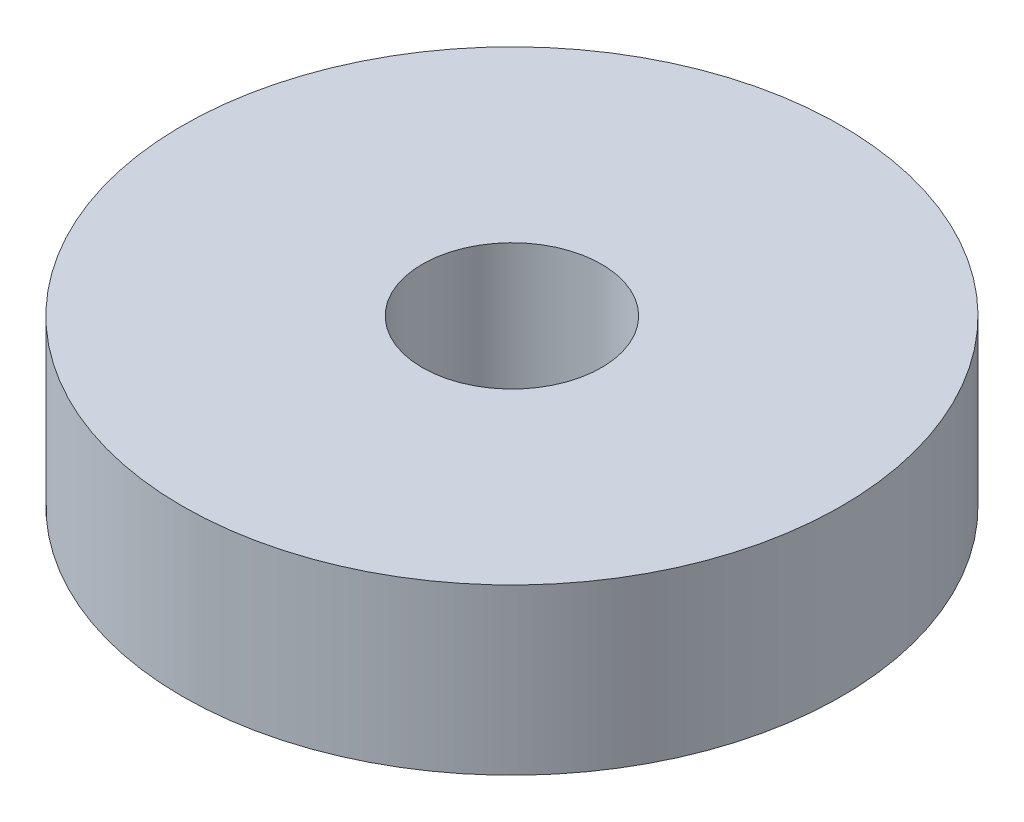
SolidWorks part; units mm, degrees
material "Acrylic (Medium-high impact)"
ref_plane "Front Plane" through (0, 0, 0) normal (0, 0, 1) x (1, 0, 0)
ref_plane "Top Plane" through (0, 0, 0) normal (0, 1, 0) x (1, 0, 0)
ref_plane "Right Plane" through (0, 0, 0) normal (1, 0, 0) x (0, 0, -1)
sketch "Sketch1" plane through (0, 0, 0) normal (0, 1, 0) x (1, 0, 0)
  circle A0 centre (0, 0) radius 6.35
  circle A1 centre (0, 0) radius 1.143
  dimension "D1" = 2.286
  dimension "D2" = 12.7
extrude "Boss-Extrude1" add sketch "Sketch1" along normal blind 3.175
hole_wizard "#8-32 Tapped Hole1" positions "Sketch3" profile "Sketch2" tap size "#8-32" standard "ANSI Inch" end condition through all
sketch "Sketch3" plane through (0, 3.175, 0) normal (0, 1, 0) x (1, 0, 0)
  point P0 (0, 0)
sketch "Sketch2" plane through (0, 3.175, 0) normal (1, 0, 0) x (0, 0, 1)
  line L0 (0, 0) -> (0, 3.175)
  line L1 (0, 3.175) -> (1.7272, 3.175)
  line L2 (1.7272, 3.175) -> (1.7272, 0)
  line L5 (1.7272, 0) -> (0, 0)
  line L11 (0, -6.35) -> (0, 107.95) construction
  dimension "Thru Tap Drill Dia." = 3.4544
  dimension "Thru Tap Drill Depth" = 3.175
cosmetic thread "Hole Thread1" parameters "D2"=4.1656
